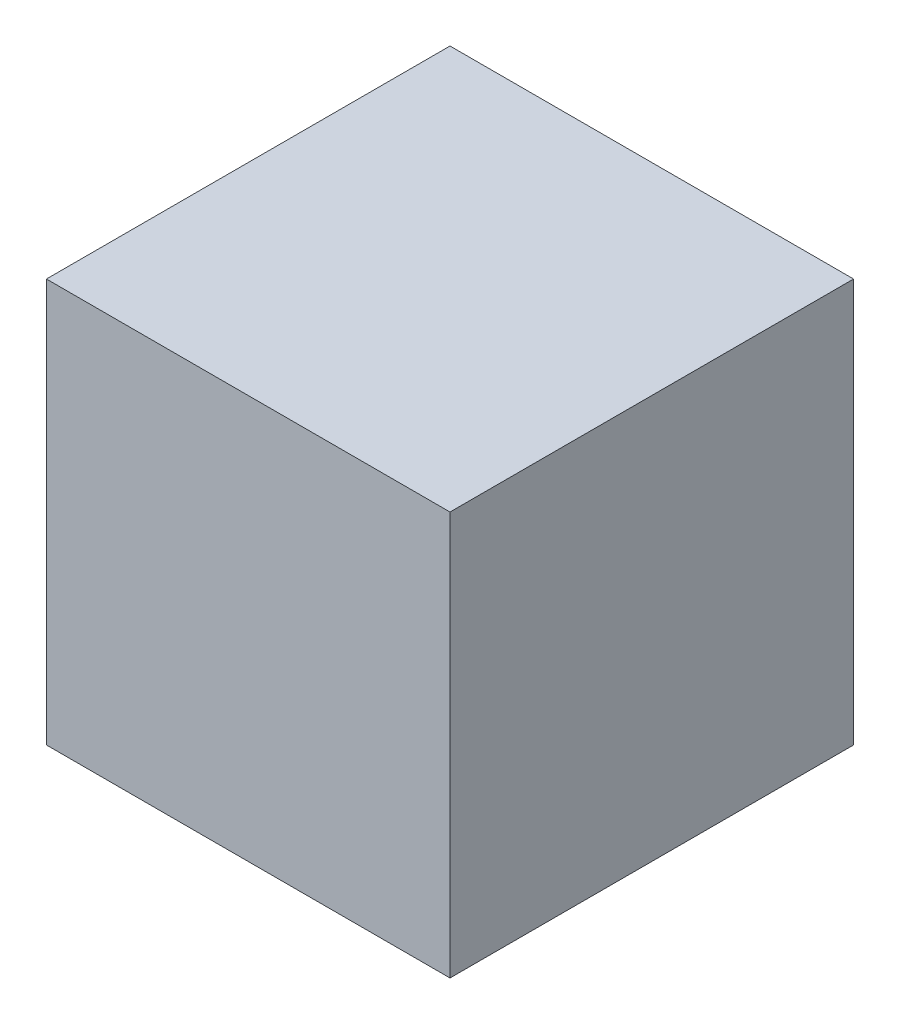
SolidWorks part; units mm, degrees
ref_plane "Front Plane" through (0, 0, 0) normal (0, 0, 1) x (1, 0, 0)
ref_plane "Top Plane" through (0, 0, 0) normal (0, 1, 0) x (1, 0, 0)
ref_plane "Right Plane" through (0, 0, 0) normal (1, 0, 0) x (0, 0, -1)
sketch "Sketch1" plane through (0, 0, 0) normal (0, 0, 1) x (1, 0, 0)
  line L1 (-50, 50) -> (50, 50)
  line L2 (-50, 50) -> (-50, -50)
  line L3 (-50, -50) -> (50, -50)
  line L4 (50, 50) -> (50, -50)
  line L5 (-50, 50) -> (50, -50) construction
  line L6 (-50, -50) -> (50, 50) construction
  point P0 (0, 0)
  dimension "D1" = 100
extrude "Boss-Extrude1" add sketch "Sketch1" along normal mid plane 100
